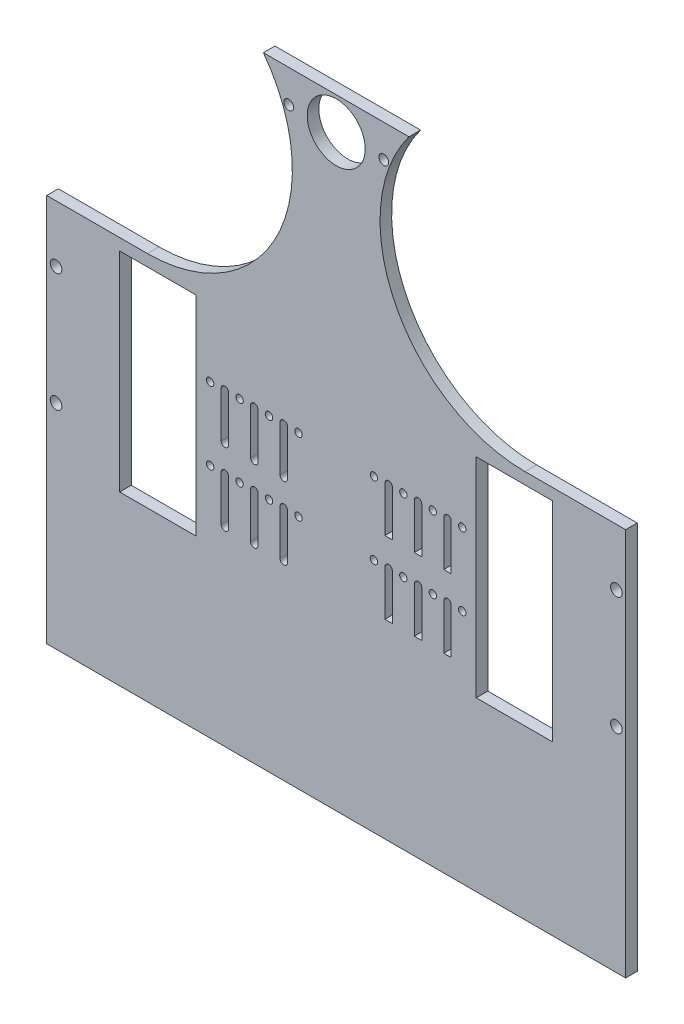
SolidWorks part; units mm, degrees
ref_plane "Front Plane" through (0, 0, 0) normal (0, 0, 1) x (1, 0, 0)
ref_plane "Top Plane" through (0, 0, 0) normal (0, 1, 0) x (1, 0, 0)
ref_plane "Right Plane" through (0, 0, 0) normal (1, 0, 0) x (0, 0, -1)
sketch "Sketch1" plane through (0, 0, 0) normal (0, 0, 1) x (1, 0, 0)
  line L0 (124.8, 0) -> (124.8, -350.4) construction
  line L1 (0, 0) -> (249.6, 0)
  line L2 (0, 0) -> (0, -350.4)
  line L3 (0, -350.4) -> (249.6, -350.4)
  line L4 (249.6, 0) -> (249.6, -350.4)
  line L9 (185.16, -105) -> (218.16, -105)
  line L10 (185.16, -105) -> (185.16, -195)
  line L11 (185.16, -195) -> (218.16, -195)
  line L12 (218.16, -105) -> (218.16, -195)
  line L13 (179.16, -150) -> (228.95, -150) construction
  line L14 (141.06, -134.375) -> (147.41, -134.375) construction
  line L15 (145.3, -14) -> (104.3, -14) construction
  line L21 (179.16, -150) -> (218.16, -150) construction
  line L25 (141.06, -165.625) -> (147.41, -165.625) construction
  line L32 (147.41, -134.375) -> (147.41, -139.375) construction
  line L33 (145.8225, -134.375) -> (145.8225, -154.0546)
  line L34 (148.9975, -134.375) -> (148.9975, -154.0546)
  line L35 (160.11, -134.375) -> (160.11, -139.375) construction
  line L36 (158.52, -134.375) -> (158.52, -154.0546)
  line L37 (161.7, -134.375) -> (161.7, -154.0546)
  line L38 (172.81, -134.375) -> (172.81, -139.375) construction
  line L39 (171.22, -134.375) -> (171.22, -154.0546)
  line L40 (174.4, -134.375) -> (174.4, -154.0546)
  line L41 (147.41, -134.375) -> (153.76, -134.375) construction
  line L42 (153.76, -134.375) -> (160.11, -134.375) construction
  line L43 (160.11, -134.375) -> (166.46, -134.375) construction
  line L44 (166.46, -134.375) -> (172.81, -134.375) construction
  line L45 (172.81, -134.375) -> (179.16, -134.375) construction
  line L48 (228.95, -150) -> (147.41, -150) construction
  line L52 (204.16, -105) -> (204.16, -195) construction
  line L53 (194.16, -105) -> (214.16, -105) construction
  line L54 (194.16, -105) -> (194.16, -195) construction
  line L55 (194.16, -195) -> (214.16, -195) construction
  line L56 (214.16, -105) -> (214.16, -195) construction
  line L62 (147.41, -165.625) -> (147.41, -170.625) construction
  line L65 (145.8225, -165.625) -> (145.8225, -185.3046)
  line L68 (148.9975, -165.625) -> (148.9975, -185.3046)
  line L71 (160.11, -165.625) -> (160.11, -170.625) construction
  line L78 (158.52, -165.625) -> (158.52, -185.3046)
  line L79 (161.7, -165.625) -> (161.7, -185.3046)
  line L80 (172.81, -165.625) -> (172.81, -170.625) construction
  line L83 (171.22, -165.625) -> (171.22, -185.3046)
  line L87 (147.41, -150) -> (102.19, -150) construction
  line L90 (179.16, -134.375) -> (179.16, -165.625) construction
  line L93 (147.41, -134.375) -> (147.41, -150) construction
  line L102 (245.6, -124.5) -> (245.6, -175.5) construction
  line L103 (218.16, -150) -> (245.6, -150) construction
  line L105 (174.4, -165.625) -> (174.4, -185.3046)
  line L106 (147.41, -165.625) -> (153.76, -165.625) construction
  line L107 (153.76, -165.625) -> (160.11, -165.625) construction
  line L108 (160.11, -165.625) -> (166.46, -165.625) construction
  line L109 (166.46, -165.625) -> (172.81, -165.625) construction
  line L110 (172.81, -165.625) -> (179.16, -165.625) construction
  line L111 (102.19, -134.375) -> (102.19, -154.0546) construction
  line L112 (103.7775, -134.375) -> (103.7775, -154.0546)
  line L113 (100.6025, -134.375) -> (100.6025, -154.0546)
  line L114 (89.49, -134.375) -> (89.49, -154.0546) construction
  line L115 (91.08, -134.375) -> (91.08, -154.0546)
  line L116 (87.9, -134.375) -> (87.9, -154.0546)
  line L117 (76.79, -134.375) -> (76.79, -154.0546) construction
  line L118 (78.38, -134.375) -> (78.38, -154.0546)
  line L119 (75.2, -134.375) -> (75.2, -154.0546)
  line L120 (102.19, -165.625) -> (102.19, -185.3046) construction
  line L121 (103.7775, -165.625) -> (103.7775, -185.3046)
  line L122 (100.6025, -165.625) -> (100.6025, -185.3046)
  line L123 (89.49, -165.625) -> (89.49, -185.3046) construction
  line L124 (91.08, -165.625) -> (91.08, -185.3046)
  line L125 (87.9, -165.625) -> (87.9, -185.3046)
  line L126 (76.79, -165.625) -> (76.79, -185.3046) construction
  line L127 (78.38, -165.625) -> (78.38, -185.3046)
  line L128 (75.2, -165.625) -> (75.2, -185.3046)
  line L129 (76.79, -165.625) -> (70.44, -165.625) construction
  line L130 (83.14, -165.625) -> (76.79, -165.625) construction
  line L131 (89.49, -165.625) -> (83.14, -165.625) construction
  line L132 (95.84, -165.625) -> (89.49, -165.625) construction
  line L133 (102.19, -165.625) -> (95.84, -165.625) construction
  line L134 (31.44, -150) -> (4, -150) construction
  line L135 (4, -124.5) -> (4, -175.5) construction
  line L136 (102.19, -134.375) -> (102.19, -150) construction
  line L137 (70.44, -134.375) -> (70.44, -165.625) construction
  line L139 (35.44, -105) -> (35.44, -195) construction
  line L140 (55.44, -195) -> (35.44, -195) construction
  line L141 (55.44, -105) -> (55.44, -195) construction
  line L142 (55.44, -105) -> (35.44, -105) construction
  line L143 (45.44, -105) -> (45.44, -195) construction
  line L144 (20.65, -150) -> (102.19, -150) construction
  line L145 (76.79, -134.375) -> (70.44, -134.375) construction
  line L146 (83.14, -134.375) -> (76.79, -134.375) construction
  line L147 (89.49, -134.375) -> (83.14, -134.375) construction
  line L148 (95.84, -134.375) -> (89.49, -134.375) construction
  line L149 (102.19, -134.375) -> (95.84, -134.375) construction
  line L150 (108.54, -165.625) -> (102.19, -165.625) construction
  line L151 (70.44, -150) -> (31.44, -150) construction
  line L152 (108.54, -134.375) -> (102.19, -134.375) construction
  line L153 (70.44, -150) -> (20.65, -150) construction
  line L154 (31.44, -105) -> (31.44, -195)
  line L155 (64.44, -195) -> (31.44, -195)
  line L156 (64.44, -105) -> (64.44, -195)
  line L157 (64.44, -105) -> (31.44, -105)
  arc A6 (174.4, -134.375) -> (171.22, -134.375) centre (172.81, -134.375) cw construction
  arc A7 (171.22, -134.375) -> (174.4, -134.375) centre (172.81, -134.375) cw
  arc A10 (158.52, -134.375) -> (161.7, -134.375) centre (160.11, -134.375) cw
  arc A11 (161.7, -134.375) -> (158.52, -134.375) centre (160.11, -134.375) cw construction
  arc A14 (145.8225, -134.375) -> (148.9975, -134.375) centre (147.41, -134.375) cw
  arc A15 (148.9975, -134.375) -> (145.8225, -134.375) centre (147.41, -134.375) cw construction
  circle A38 centre (104.3, -14) radius 2.1
  arc A39 (148.9975, -154.0546) -> (145.8225, -154.0546) centre (147.41, -139.375) cw
  arc A41 (161.7, -154.0546) -> (158.52, -154.0546) centre (160.11, -139.375) cw
  arc A43 (174.4, -154.0546) -> (171.22, -154.0546) centre (172.81, -139.375) cw
  circle A84 centre (245.6, -124.5) radius 2.5
  circle A85 centre (245.6, -175.5) radius 2.5
  circle A109 centre (145.3, -14) radius 2.1
  circle A179 centre (179.16, -134.375) radius 1.59
  arc A182 (174.4, -165.625) -> (171.22, -165.625) centre (172.81, -165.625) cw construction
  arc A183 (171.22, -165.625) -> (174.4, -165.625) centre (172.81, -165.625) cw
  arc A184 (158.52, -165.625) -> (161.7, -165.625) centre (160.11, -165.625) cw
  arc A185 (161.7, -165.625) -> (158.52, -165.625) centre (160.11, -165.625) cw construction
  arc A188 (145.8225, -165.625) -> (148.9975, -165.625) centre (147.41, -165.625) cw
  arc A189 (148.9975, -165.625) -> (145.8225, -165.625) centre (147.41, -165.625) cw construction
  arc A193 (148.9975, -185.3046) -> (145.8225, -185.3046) centre (147.41, -170.625) cw
  arc A195 (161.7, -185.3046) -> (158.52, -185.3046) centre (160.11, -170.625) cw
  arc A197 (174.4, -185.3046) -> (171.22, -185.3046) centre (172.81, -170.625) cw
  circle A198 centre (179.16, -165.625) radius 1.59
  circle A199 centre (124.8, -14) radius 12.5
  circle A200 centre (141.06, -134.375) radius 1.59
  circle A201 centre (153.76, -134.375) radius 1.59
  circle A202 centre (166.46, -134.375) radius 1.59
  circle A203 centre (141.06, -165.625) radius 1.59
  circle A204 centre (153.76, -165.625) radius 1.59
  circle A205 centre (166.46, -165.625) radius 1.59
  arc A206 (103.7775, -134.375) -> (100.6025, -134.375) centre (102.19, -134.375) ccw
  arc A207 (100.6025, -154.0546) -> (103.7775, -154.0546) centre (102.19, -154.0546) ccw
  arc A208 (91.08, -134.375) -> (87.9, -134.375) centre (89.49, -134.375) ccw
  arc A209 (87.9, -154.0546) -> (91.08, -154.0546) centre (89.49, -154.0546) ccw
  arc A210 (78.38, -134.375) -> (75.2, -134.375) centre (76.79, -134.375) ccw
  arc A211 (75.2, -154.0546) -> (78.38, -154.0546) centre (76.79, -154.0546) ccw
  arc A212 (103.7775, -165.625) -> (100.6025, -165.625) centre (102.19, -165.625) ccw
  arc A213 (100.6025, -185.3046) -> (103.7775, -185.3046) centre (102.19, -185.3046) ccw
  arc A214 (91.08, -165.625) -> (87.9, -165.625) centre (89.49, -165.625) ccw
  arc A215 (87.9, -185.3046) -> (91.08, -185.3046) centre (89.49, -185.3046) ccw
  arc A216 (78.38, -165.625) -> (75.2, -165.625) centre (76.79, -165.625) ccw
  arc A217 (75.2, -185.3046) -> (78.38, -185.3046) centre (76.79, -185.3046) ccw
  arc A218 (100.6025, -165.625) -> (103.7775, -165.625) centre (102.19, -165.625) ccw construction
  arc A219 (87.9, -165.625) -> (91.08, -165.625) centre (89.49, -165.625) ccw construction
  arc A220 (75.2, -165.625) -> (78.38, -165.625) centre (76.79, -165.625) ccw construction
  arc A221 (100.6025, -134.375) -> (103.7775, -134.375) centre (102.19, -134.375) ccw construction
  arc A222 (87.9, -134.375) -> (91.08, -134.375) centre (89.49, -134.375) ccw construction
  arc A223 (75.2, -134.375) -> (78.38, -134.375) centre (76.79, -134.375) ccw construction
  circle A224 centre (83.14, -165.625) radius 1.59
  circle A225 centre (95.84, -165.625) radius 1.59
  circle A226 centre (108.54, -165.625) radius 1.59
  circle A227 centre (83.14, -134.375) radius 1.59
  circle A228 centre (95.84, -134.375) radius 1.59
  circle A229 centre (108.54, -134.375) radius 1.59
  circle A230 centre (70.44, -165.625) radius 1.59
  circle A234 centre (70.44, -134.375) radius 1.59
  circle A236 centre (4, -175.5) radius 2.5
  circle A237 centre (4, -124.5) radius 2.5
  point P64 (147.41, -150)
  point P65 (102.19, -144.2148)
  point P69 (228.95, -150)
  point P71 (221, -87.34)
  point P76 (233.7, -87.34)
  point P78 (221, -54.5)
  point P82 (233.7, -54.5)
  point P86 (246.4, -54.5)
  point P93 (179.16, -150)
  point P97 (246.4, -87.34)
  point P104 (89.49, -144.2148)
  point P111 (76.79, -144.2148)
  point P119 (102.19, -175.4648)
  point P126 (89.49, -175.4648)
  point P133 (76.79, -175.4648)
  point P155 (124.8, -76.5574)
  point P166 (124.8, -150)
  point P183 (124.8, -76.5574)
  point P199 (70.44, -150)
  point P200 (20.65, -150)
  point P201 (102.19, -150)
  dimension "D5" = 20
  dimension "D10" = 5
  dimension "D12" = 3.18
  dimension "D15" = 5
  dimension "D16" = 5
  dimension "D19" = 3.18
  dimension "D20" = 1.5875
  dimension "D21" = 3.18
  dimension "D22" = 1.59
  dimension "D23" = 3.18
  dimension "D24" = 1.59
  dimension "D25" = 3.18
  dimension "D33" = 3.18
  dimension "D34" = 5
  dimension "D35" = 4.2
  dimension "D32" = 1.5875
  dimension "D36" = 1.59
  dimension "D37" = 3.18
  dimension "D39" = 1.59
  dimension "D47" = 3.18
  dimension "D49" = 25
  dimension "D51" = 4.2
  dimension "D1" = 249.6
  dimension "D2" = 350.4
  dimension "D3" = 4
  dimension "D4" = 90
  dimension "D6" = 90
  dimension "D7" = 9
  dimension "D8" = 6
  dimension "D9" = 5
  dimension "D11" = 6.35
  dimension "D13" = 6.35
  dimension "D14" = 89.36
  dimension "D17" = 25.5
  dimension "D18" = 4
  dimension "D26" = 5
  dimension "D27" = 6.35
  dimension "D28" = 6.35
  dimension "D29" = 6.35
  dimension "D30" = 6.35
  dimension "D31" = 6.35
  dimension "D38" = 105
  dimension "D40" = 5
  dimension "D41" = 6.35
  dimension "D42" = 6.35
  dimension "D43" = 6.35
  dimension "D44" = 6.35
  dimension "D45" = 6.35
  dimension "D46" = 5
  dimension "D48" = 31.25
  dimension "D50" = 20.5
  dimension "14" = 14
extrude "Boss-Extrude1" add sketch "Sketch1" along normal blind 5
sketch "Sketch11" plane through (0, 0, 5) normal (0, 0, 1) x (1, 0, 0)
  line L1 (0, 0) -> (0, -350.4) construction
  line L2 (249.6, -350.4) -> (249.6, 0) construction
  line L3 (0, -100) -> (249.6, -100) construction
  line L6 (0, -350.4) -> (249.6, -350.4) construction
  line L8 (249.6, 0) -> (0, 0) construction
  line L9 (189.8, 0) -> (189.8, -350.4) construction
  line L10 (244.6, 0) -> (244.6, -350.4) construction
  line L11 (184.8, 0) -> (184.8, -350.4) construction
  line L19 (0, -105) -> (249.6, -105) construction
  line L22 (124.8, 0) -> (124.8, -350.4) construction
  line L23 (64.44, -105) -> (31.44, -105) construction
  line L27 (161.7, -154.0546) -> (161.7, -134.375) construction
  line L30 (75.2, -134.375) -> (75.2, -154.0546) construction
  line L31 (5, -350.4) -> (5, 0) construction
  line L33 (64.8, -350.4) -> (64.8, 0) construction
  line L34 (-280.156, -400.7943) -> (540.6546, 73.101) construction
  line L35 (59.8, 0) -> (59.8, -350.4) construction
  line L36 (-311.8259, -280.5148) -> (435.1308, 150.7409) construction
  line L37 (382.6504, -177.2987) -> (-156.0003, 133.6914) construction
  line L38 (370.9591, -309.1128) -> (-242.9721, 45.3405) construction
  circle A11 centre (124.8, -262.4248) radius 60 construction
  circle A12 centre (124.8, -262.4248) radius 62.5 construction
  circle A13 centre (209.42, -146.5661) radius 24.62 construction
  circle A14 centre (82.49, -73.2831) radius 60 construction
  circle A15 centre (124.8, 0) radius 24.62 construction
  circle A17 centre (40.18, -146.5661) radius 24.62 construction
  circle A18 centre (167.11, -73.2831) radius 60 construction
  dimension "D4" = 5
  dimension "D5" = 125
  dimension "D3" = 120
  dimension "D9" = 5
  dimension "D10" = 120
  dimension "D11" = 5
  dimension "D12" = 5
  dimension "D13" = 49.24
  dimension "D8" = 49.24
  dimension "D6" = 120
  dimension "D2" = 49.24
  dimension "D7" = 5
sketch "Sketch13" plane through (0, 0, 5) normal (0, 0, 1) x (1, 0, 0)
  line L0 (0, -100) -> (249.6, -100) construction
  line L1 (43.4029, -100) -> (0, -100)
  line L2 (43.4029, 25) -> (0, 25)
  line L3 (206.1971, 25) -> (249.6, 25)
  line L4 (0, 25) -> (0, -100)
  line L5 (249.6, 25) -> (249.6, -100)
  line L6 (0, -105) -> (249.6, -105) construction
  line L7 (64.44, -105) -> (31.44, -105) construction
  line L8 (0, 0) -> (0, -350.4) construction
  line L9 (0, 0) -> (0, -350.4) construction
  line L10 (249.6, -350.4) -> (249.6, 0) construction
  line L11 (206.1971, -100) -> (249.6, -100)
  arc A0 (43.4029, -100) -> (43.4029, 25) centre (43.4029, -37.5) ccw
  arc A1 (206.1971, 25) -> (206.1971, -100) centre (206.1971, -37.5) ccw
  circle A2 centre (43.4029, -37.5) radius 65 construction
  circle A3 centre (206.1971, -37.5) radius 65 construction
  circle A4 centre (124.8, 0) radius 24.62 construction
  dimension "D2" = 130
  dimension "D3" = 62.5
  dimension "D4" = 130
  dimension "D5" = 62.5
  dimension "D1" = 5
sketch "Sketch12" plane through (0, -350.4, 0) normal (0, -1, 0) x (1, 0, 0)
  line L0 (0, 0) -> (249.6, 0)
  line L1 (0, 0) -> (0, 5)
  line L2 (249.6, 0) -> (249.6, 5)
  line L3 (0, 5) -> (249.6, 5)
  line L5 (0, 5) -> (249.6, 5) construction
extrude "Cut-Extrude2" cut sketch "Sketch12" against normal blind 83
extrude "Cut-Extrude3" cut sketch "Sketch13" against normal through all
